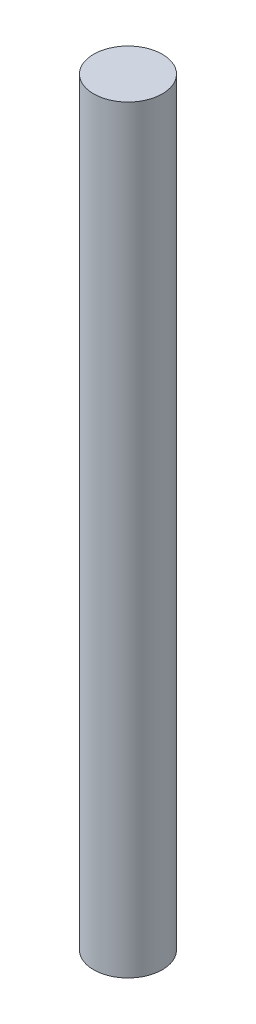
SolidWorks part; units mm, degrees
ref_plane "Front Plane" through (0, 0, 0) normal (0, 0, 1) x (1, 0, 0)
ref_plane "Top Plane" through (0, 0, 0) normal (0, 1, 0) x (1, 0, 0)
ref_plane "Right Plane" through (0, 0, 0) normal (1, 0, 0) x (0, 0, -1)
sketch "Sketch4" plane through (0, 0, 0) normal (0, 1, 0) x (1, 0, 0)
  circle A0 centre (-115.3436, 28.3684) radius 11.25
  dimension "D1" = 22.5
extrude "Boss-Extrude1" add sketch "Sketch4" along normal blind 248.5
